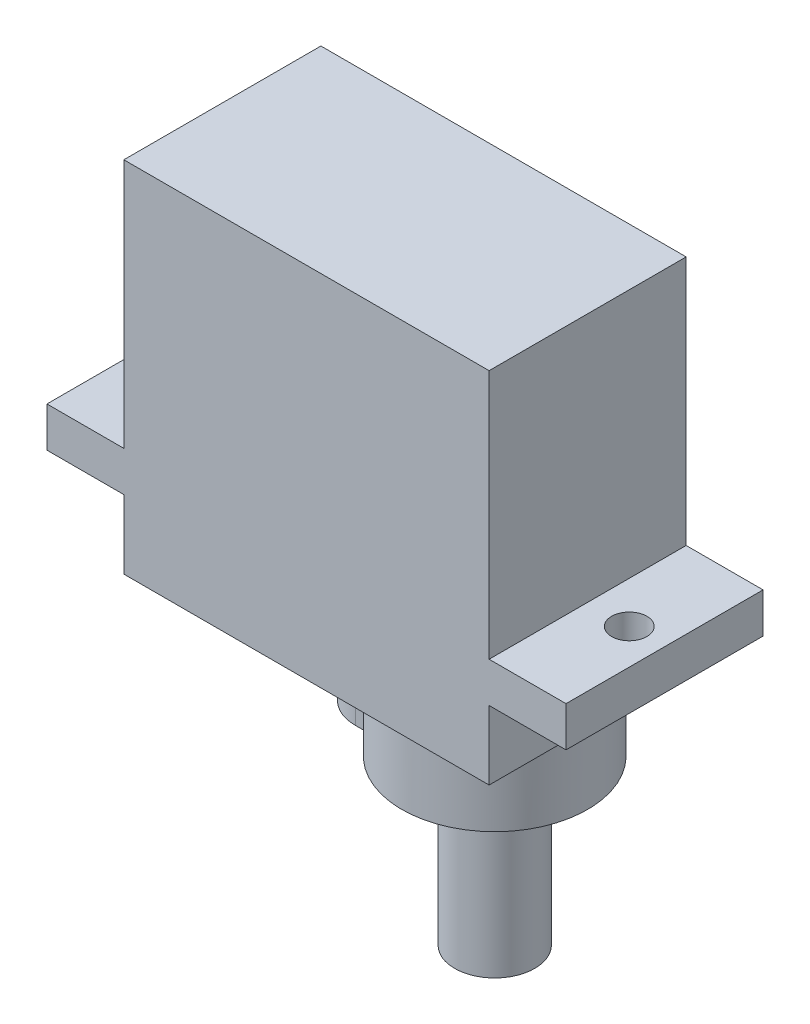
SolidWorks part; units mm, degrees
ref_plane "前基準面" through (0, 0, 0) normal (0, 0, 1) x (1, 0, 0)
ref_plane "上基準面" through (0, 0, 0) normal (0, 1, 0) x (1, 0, 0)
ref_plane "右基準面" through (0, 0, 0) normal (1, 0, 0) x (0, 0, -1)
sketch "Sketch1" plane through (0, 0, 0) normal (0, 0, 1) x (1, 0, 0)
  line L0 (-16.2, 0) -> (-11.4, 0)
  line L1 (16.2, 0) -> (16.2, 2.5)
  line L2 (16.2, 2.5) -> (11.4, 2.5)
  line L3 (11.4, 2.5) -> (11.4, 18.1)
  line L4 (11.4, 18.1) -> (-11.4, 18.1)
  line L5 (-11.4, 18.1) -> (-11.4, 2.5)
  line L6 (-11.4, 2.5) -> (-16.2, 2.5)
  line L7 (-16.2, 2.5) -> (-16.2, 0)
  line L8 (0, 18.1) -> (0, 0) construction
  line L9 (-11.4, 0) -> (-11.4, -4.3)
  line L10 (-11.4, -4.3) -> (11.4, -4.3)
  line L11 (11.4, -4.3) -> (11.4, 0)
  line L12 (11.4, 0) -> (16.2, 0)
  line L13 (-11.4, 0) -> (11.4, 0) construction
  dimension "D1" = 2.5
  dimension "D2" = 15.6
  dimension "D3" = 32.4
  dimension "D4" = 2.5
  dimension "D5" = 22.8
  dimension "D6" = 4.3
  dimension "D7" = 4.8
extrude "Boss-Extrude1" add sketch "Sketch1" along normal blind 12.3
sketch "Sketch2" plane through (0, -4.3, 0) normal (0, -1, 0) x (1, 0, 0)
  line L0 (16.2, 6.15) -> (5.6, 6.15) construction
  line L1 (16.2, 12.3) -> (16.2, 0) construction
  line L2 (-0.4, 8.85) -> (0.4668, 8.85)
  line L3 (5.6, 6.15) -> (-0.4, 6.15) construction
  line L4 (-0.4, 3.45) -> (0.4668, 3.45)
  line L5 (11.4, 12.3) -> (11.4, 0) construction
  arc A0 (0.4668, 3.45) -> (0.4668, 8.85) centre (5.6, 6.15) ccw
  arc A1 (-0.4, 8.85) -> (-0.4, 3.45) centre (-0.4, 6.15) ccw
  dimension "D1" = 11.6
  dimension "D3" = 5.4
  dimension "D4" = 6
extrude "Boss-Extrude2" add sketch "Sketch2" along normal blind 4.4
sketch "Sketch3" plane through (0, 2.5, 0) normal (0, 1, 0) x (1, 0, 0)
  line L0 (-16.2, -6.15) -> (-14, -6.15) construction
  line L1 (-16.2, -12.3) -> (-16.2, 0) construction
  line L2 (16.2, -6.15) -> (14, -6.15) construction
  line L3 (16.2, -12.3) -> (16.2, 0) construction
  circle A0 centre (-14, -6.15) radius 1.1
  circle A1 centre (14, -6.15) radius 1.1
  dimension "D1" = 2.2
  dimension "D2" = 2.2
  dimension "D5" = 28
  dimension "D3" = 2.2
  dimension "D4" = 2.2
extrude "Cut-Extrude1" cut sketch "Sketch3" against normal blind 8
sketch "草圖1" plane through (0, -8.7, 0) normal (0, -1, 0) x (-1, 0, 0)
  circle A0 centre (-5.6, -6.15) radius 2.5
  dimension "D1" = 5
extrude "填料-伸長1" add sketch "草圖1" along normal blind 10.2406 separate body
